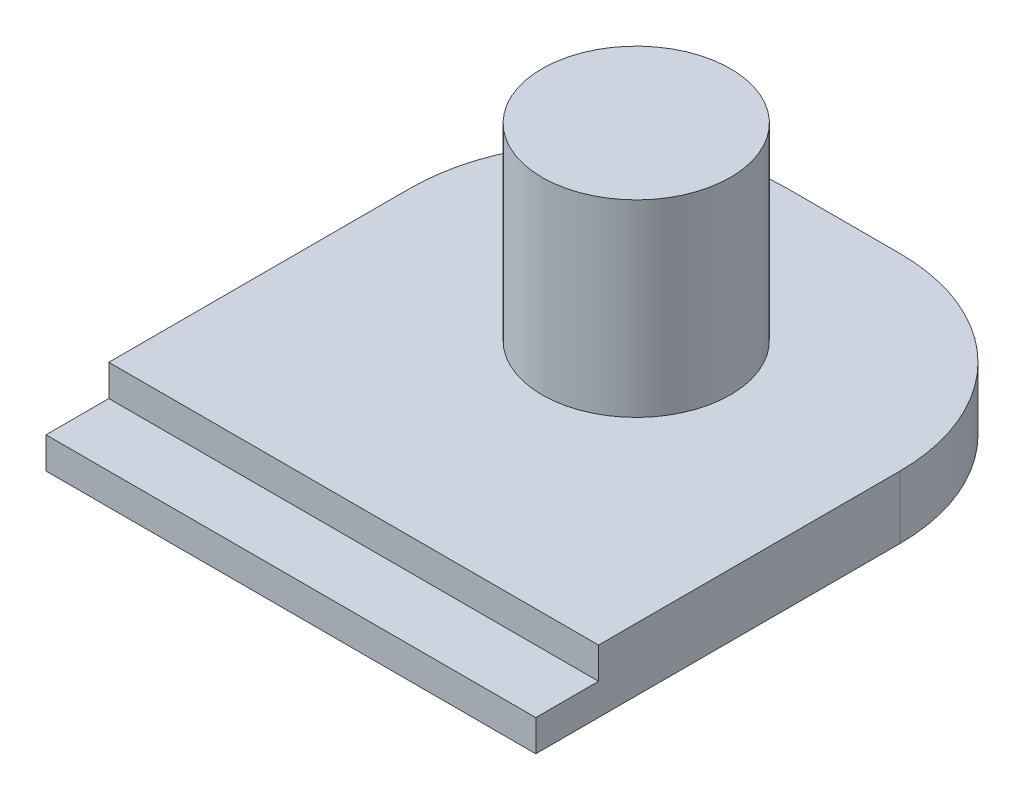
SolidWorks part; units mm, degrees
ref_plane "Front Plane" through (0, 0, 0) normal (0, 0, 1) x (1, 0, 0)
ref_plane "Top Plane" through (0, 0, 0) normal (0, 1, 0) x (1, 0, 0)
ref_plane "Right Plane" through (0, 0, 0) normal (1, 0, 0) x (0, 0, -1)
sketch "Sketch1" plane through (0, 0, 0) normal (0, 1, 0) x (1, 0, 0)
  line L1 (0, 0) -> (7.8, 0)
  line L2 (0, 0) -> (0, 5.8)
  line L3 (3, 8.8) -> (4.8, 8.8)
  line L4 (7.8, 0) -> (7.8, 5.8)
  arc A0 (3, 8.8) -> (0, 5.8) centre (3, 5.8) ccw
  arc A1 (7.8, 5.8) -> (4.8, 8.8) centre (4.8, 5.8) ccw
  point P9 (7.8, 8.8)
  dimension "D3" = 3
  dimension "D1" = 7.8
  dimension "D2" = 8.8
extrude "Boss-Extrude1" add sketch "Sketch1" along normal blind 1
sketch "Sketch2" plane through (0, 1, 0) normal (0, 1, 0) x (1, 0, 0)
  line L0 (0, 0) -> (7.8, 0) construction
  circle A0 centre (3.9, 5.5) radius 1.5
  point P4 (3.9, 0)
  dimension "D1" = 3
  dimension "D2" = 5.5
extrude "Boss-Extrude2" add sketch "Sketch2" along normal blind 3
sketch "Sketch3" plane through (0, 1, 0) normal (0, 1, 0) x (1, 0, 0)
  line L0 (7.8, 0) -> (7.8, 5.8) construction
  line L1 (0, 0) -> (7.8, 0)
  line L2 (0, 0) -> (0, 1)
  line L3 (0, 1) -> (7.8, 1)
  line L4 (7.8, 0) -> (7.8, 1)
  dimension "D1" = 1
extrude "Cut-Extrude1" cut sketch "Sketch3" against normal blind 0.5
